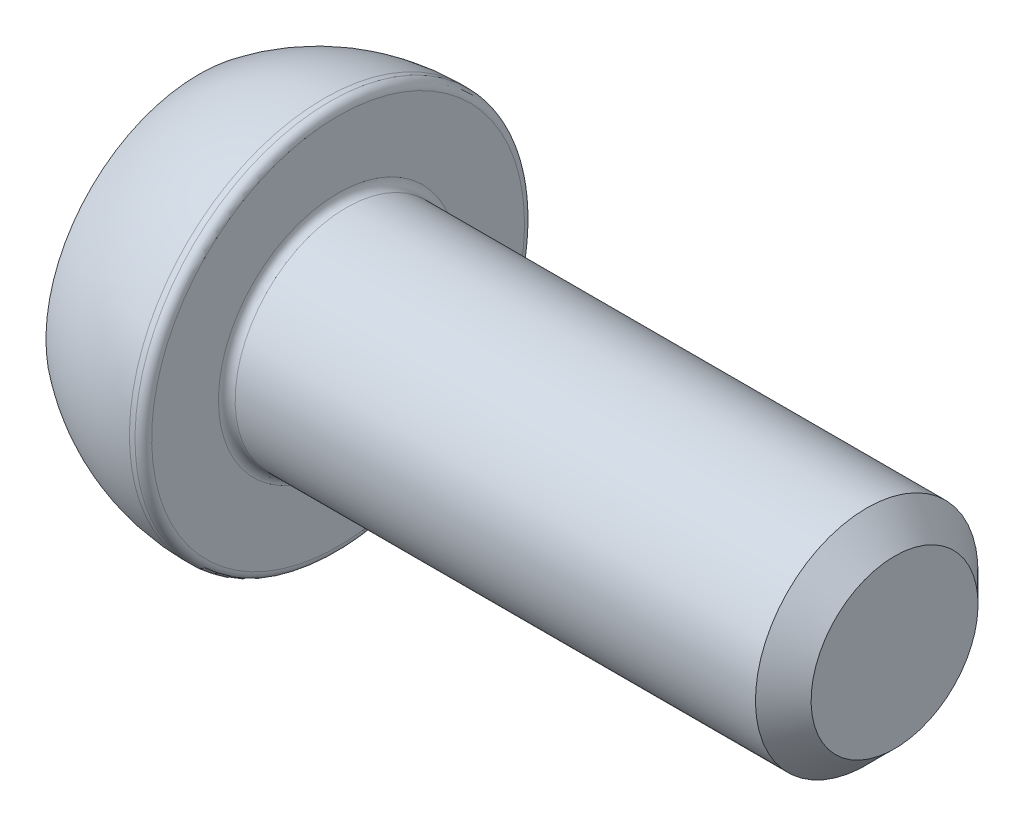
SolidWorks part; units mm, degrees
ref_plane "Спереди" through (0, 0, 0) normal (0, 0, 1) x (1, 0, 0)
ref_plane "Сверху" through (0, 0, 0) normal (0, 1, 0) x (1, 0, 0)
ref_plane "Справа" through (0, 0, 0) normal (1, 0, 0) x (0, 0, -1)
sketch "Эскиз1" plane through (0, 0, 0) normal (0, 0, 1) x (1, 0, 0)
  line L0 (0, 0) -> (0, 5.5)
  line L1 (4.5, 7) -> (5, 7)
  line L2 (5, 7) -> (5, 4)
  line L3 (5, 4) -> (25, 4)
  line L4 (25, 4) -> (25, 0)
  line L5 (25, 0) -> (0, 0) construction
  line L6 (0, 0) -> (25, 0)
  arc A0 (0, 5.5) -> (4.5, 7) centre (4.5, -0.5) cw
  point P9 (5, 5.5)
  dimension "D1" = 0.5
  dimension "D2" = 8
  dimension "D3" = 14
  dimension "D5" = 5
  dimension "D6" = 20
revolve "Повернуть1" add sketch "Эскиз1" angle 360 about L5
cosmetic thread "Условное изображение резьбы1" parameters "D2"=6.619
sketch "Эскиз2" plane through (0, 0, 0) normal (-1, 0, 0) x (0, 0, 1)
  line L1 (1.7321, 3) -> (-1.7321, 3)
  line L2 (-1.7321, 3) -> (-3.4641, 0)
  line L3 (-3.4641, 0) -> (-1.7321, -3)
  line L4 (-1.7321, -3) -> (1.7321, -3)
  line L5 (1.7321, -3) -> (3.4641, 0)
  line L6 (3.4641, 0) -> (1.7321, 3)
  circle A0 centre (0, 0) radius 3 construction
  dimension "D1" = 6
extrude "Вырез-Вытянуть1" cut sketch "Эскиз2" against normal blind 3
fillet "Скругление1" radius 0.3 2 edges at (5, 4, 0) (5, 7, 0)
chamfer "Фаска1" distance 1 angle 45 1 edges at (25, 4, 0)
